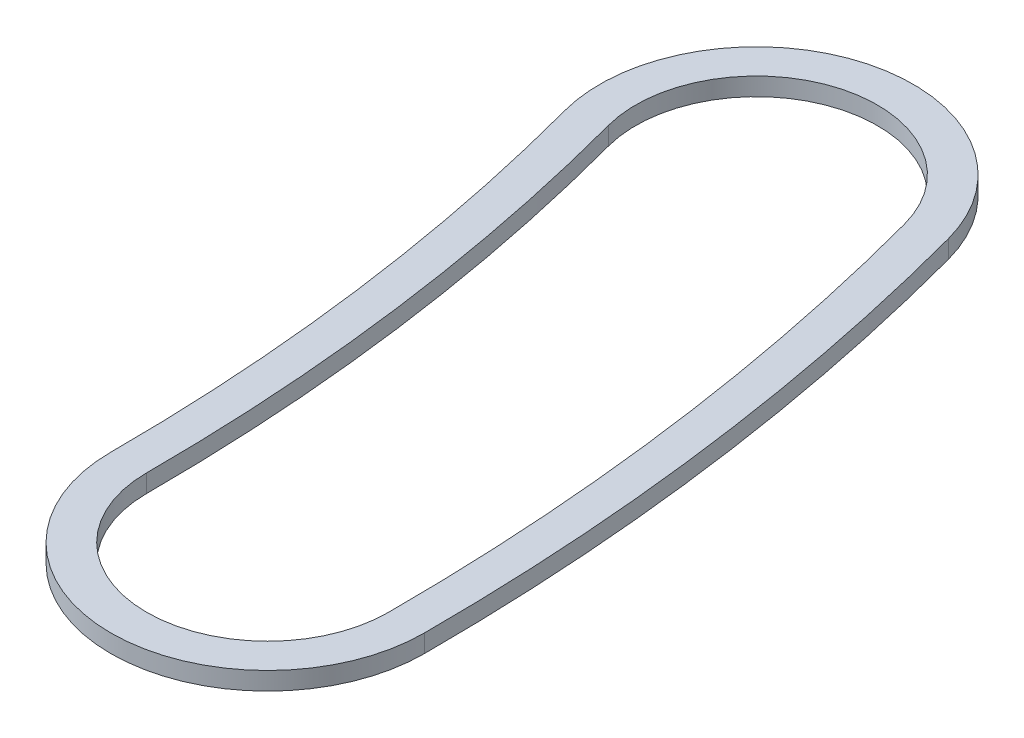
SolidWorks part; units mm, degrees
material "NBR"
ref_plane "Front Plane" through (0, 0, 0) normal (0, 0, 1) x (1, 0, 0)
ref_plane "Top Plane" through (0, 0, 0) normal (0, 1, 0) x (1, 0, 0)
ref_plane "Right Plane" through (0, 0, 0) normal (1, 0, 0) x (0, 0, -1)
sketch "Sketch1" plane through (0, 0, 0) normal (0, 1, 0) x (1, 0, 0)
  line L0 (0, 0) -> (59.6189, 15.9748) construction
  line L1 (0, 0) -> (61.722, 0) construction
  arc A0 (61.722, 0) -> (59.6189, 15.9748) centre (0, 0) ccw construction
  arc A1 (66.167, 0) -> (63.9124, 17.1253) centre (0, 0) ccw
  arc A2 (57.277, 0) -> (55.3253, 14.8244) centre (0, 0) ccw
  arc A3 (57.277, 0) -> (66.167, 0) centre (61.722, 0) ccw
  arc A4 (63.9124, 17.1253) -> (55.3253, 14.8244) centre (59.6189, 15.9748) ccw
  arc A5 (61.722, 0) -> (59.6189, 15.9748) centre (0, 0) ccw construction
  arc A6 (65.151, 0) -> (62.931, 16.8623) centre (0, 0) ccw
  arc A7 (58.293, 0) -> (56.3067, 15.0873) centre (0, 0) ccw
  arc A8 (58.293, 0) -> (65.151, 0) centre (61.722, 0) ccw
  arc A9 (62.931, 16.8623) -> (56.3067, 15.0873) centre (59.6189, 15.9748) ccw
  point P4 (61.194, 8.0563)
  point P13 (61.194, 8.0563)
  dimension "D4" = 61.722
  dimension "D3" = 4.445
  dimension "D2" = 1.016
  dimension "D1" = 15
extrude "Boss-Extrude1" add sketch "Sketch1" along normal blind 0.508
equation "\"w\"= 0.04"
equation "\"D2@Sketch1\"=\"w\""
equation "\"D3@Sketch1\"= .185 - .01 '10 thou smaller than channel rad"
